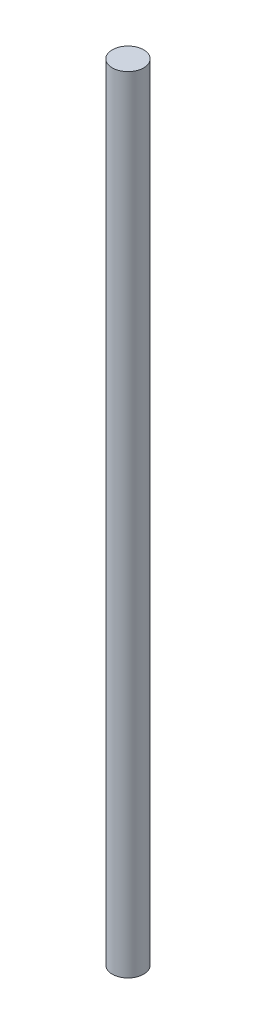
SolidWorks part; units mm, degrees
ref_plane "Front Plane" through (0, 0, 0) normal (0, 0, 1) x (1, 0, 0)
ref_plane "Top Plane" through (0, 0, 0) normal (0, 1, 0) x (1, 0, 0)
ref_plane "Right Plane" through (0, 0, 0) normal (1, 0, 0) x (0, 0, -1)
sketch "Sketch1" plane through (0, 0, 0) normal (0, 1, 0) x (1, 0, 0)
  circle A0 centre (0, 0) radius 2
extrude "Boss-Extrude1" add sketch "Sketch1" along normal blind 100
